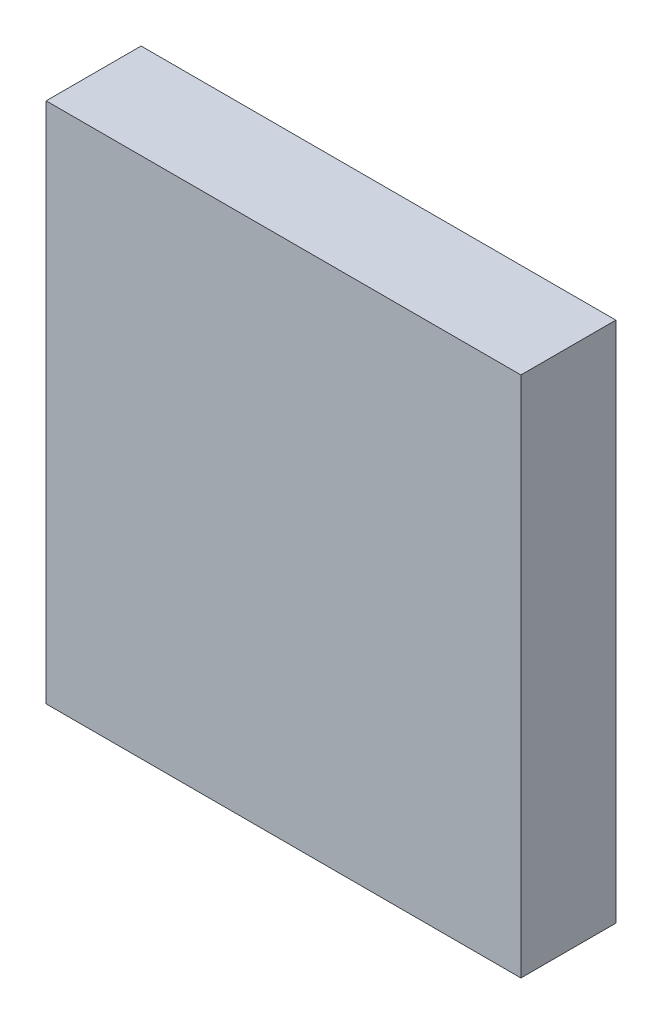
SolidWorks part; units mm, degrees
ref_plane "Front Plane" through (0, 0, 0) normal (0, 0, 1) x (1, 0, 0)
ref_plane "Top Plane" through (0, 0, 0) normal (0, 1, 0) x (1, 0, 0)
ref_plane "Right Plane" through (0, 0, 0) normal (1, 0, 0) x (0, 0, -1)
sketch "Sketch1" plane through (0, 0, 0) normal (0, 0, 1) x (1, 0, 0)
  line L0 (12.5, 13.75) -> (-12.5, -13.75) construction
  line L1 (-12.5, 13.75) -> (12.5, 13.75)
  line L2 (-12.5, 13.75) -> (-12.5, -13.75)
  line L3 (-12.5, -13.75) -> (12.5, -13.75)
  line L4 (12.5, 13.75) -> (12.5, -13.75)
  line L5 (12.5, -13.75) -> (12.5, 13.75) construction
  line L6 (12.5, -13.75) -> (0, 0) construction
  line L7 (0, 0) -> (-12.5, 13.75) construction
  dimension "D1" = 25
  dimension "D2" = 27.5
extrude "Boss-Extrude1" add sketch "Sketch1" along normal blind 5
